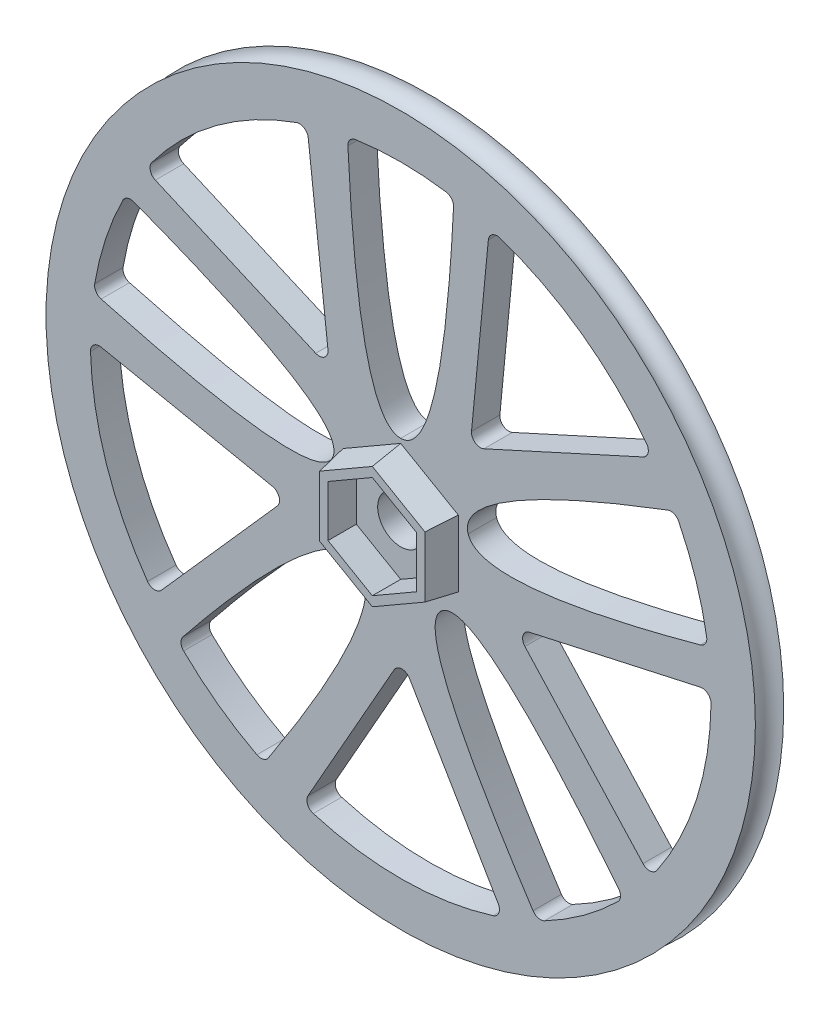
SolidWorks part; units mm, degrees
ref_plane "Front Plane" through (0, 0, 0) normal (0, 0, 1) x (1, 0, 0)
ref_plane "Top Plane" through (0, 0, 0) normal (0, 1, 0) x (1, 0, 0)
ref_plane "Right Plane" through (0, 0, 0) normal (1, 0, 0) x (0, 0, -1)
sketch "Sketch1" plane through (0, 0, 0) normal (0, 0, 1) x (1, 0, 0)
  circle A0 centre (0, 0) radius 50.8
  dimension "D1" = 101.6
extrude "Boss-Extrude1" add sketch "Sketch1" along normal mid plane 4.064
ref_axis "Axis1" through (0, 0, 17.7732) along (0, 0, -1)
sketch "Sketch2" plane through (0, 0, 0) normal (1, 0, 0) x (0, 0, -1)
  line L2 (-2.032, 50.8) -> (-2.032, -50.8) construction
  line L3 (-2.032, 50.8) -> (2.032, 50.8)
  circle A0 centre (0, 50.8) radius 2.032 construction
  arc A1 (-2.032, 50.8) -> (2.032, 50.8) centre (0, 50.8) ccw
revolve "Cut-Revolve1" cut sketch "Sketch2" angle 360 about axis through (0, 0, 17.7732) along (0, 0, -1)
sketch "Sketch3" plane through (0, 0, 0) normal (0, 0, 1) x (1, 0, 0)
  line L0 (0, 0) -> (0, 44.45) construction
  line L1 (0, 0) -> (44.45, 0) construction
  line L2 (-2.8815, 10.16) -> (2.8815, 10.16) construction
  line L3 (2.8814, 10.16) -> (-2.8815, 10.16) construction
  circle A0 centre (0, 0) radius 10.16 construction
  arc A1 (-7.62, 43.792) -> (7.62, 43.792) centre (0, 0) cw
  circle A2 centre (0, 0) radius 44.45 construction
  spline S0 degree 2 poles (0, 10.16) (6.0921, 10.16) (7.62, 43.792) knots 0 0 0 1 1 1
  spline S1 degree 2 poles (0, 10.16) (-6.0921, 10.16) (-7.62, 43.792) knots 0 0 0 1 1 1
  dimension "D1" = 20.32
  dimension "D2" = 88.9
  dimension "D3" = 15.24
extrude "Cut-Extrude1" cut sketch "Sketch3" against normal mid plane 5.08
pattern_circular "CirPattern1" count 5 over 360 about axis through (0, 0, 17.7732) along (0, 0, -1) of "Cut-Extrude1"
sketch "Sketch4" plane through (0, 0, 0) normal (0, 0, 1) x (1, 0, 0)
  line L0 (12.7, 42.5971) -> (9.9317, 13.9168)
  line L1 (9.9317, 13.9168) -> (36.1537, 25.8595)
  circle A0 centre (0, 0) radius 10.16 construction
  circle A1 centre (0, 0) radius 10.16 construction
  circle A2 centre (0, 0) radius 44.45 construction
  circle A3 centre (0, 0) radius 44.45 construction
  arc A4 (12.7, 42.5971) -> (36.1537, 25.8595) centre (0, 0) cw
  dimension "D1" = 5.08
  dimension "D2" = 5.08
  dimension "D3" = 60
extrude "Cut-Extrude2" cut sketch "Sketch4" against normal mid plane 5.08
pattern_circular "CirPattern2" count 5 over 360 about axis through (0, 0, 0) along (0, 0, 1) of "Cut-Extrude2"
fillet "Fillet1" radius 1.27 25 edges at (-16.215, -5.4213, 0) (0.1452, -17.0966, 0) (16.3047, -5.145, 0) (9.9317, 13.9168, 0) (-10.1666, 13.7461, 0) (12.7, 42.5971, 0) (36.1537, 25.8595, 0) (44.0034, 6.2854, 0) (39.2939, 20.7795, 0) (44.4368, 1.0848, 0) (35.766, -26.3932, 0) (31.905, -30.9495, 0) (19.5756, -39.9074, 0) (14.7634, -41.9266, 0) (-14.0491, -42.1714, 0) (-19.5756, -39.9074, 0) (-31.905, -30.9495, 0) (-35.3125, -26.9969, 0) (-44.4488, 0.3298, 0) (-44.0034, 6.2854, 0) (-39.2939, 20.7795, 0) (-36.5877, 25.2416, 0) (-13.4218, 42.3752, 0) (-7.62, 43.792, 0) (7.62, 43.792, 0)
sketch "Sketch5" plane through (0, 0, 2.032) normal (0, 0, 1) x (1, 0, 0)
  line L1 (-8.255, -4.766) -> (0, -9.5321)
  line L2 (0, -9.5321) -> (8.255, -4.766)
  line L3 (8.255, -4.766) -> (8.255, 4.766)
  line L4 (8.255, 4.766) -> (0, 9.5321)
  line L5 (0, 9.5321) -> (-8.255, 4.766)
  line L6 (-8.255, 4.766) -> (-8.255, -4.766)
  line L7 (0, 0) -> (0, 44.45) construction
  circle A0 centre (0, 0) radius 8.255 construction
  dimension "D1" = 16.51
extrude "Boss-Extrude2" add sketch "Sketch5" along normal blind 4.064 draft 10
sketch "Sketch6" plane through (0, 0, 6.096) normal (0, 0, 1) x (1, 0, 0)
  line L0 (0, 0) -> (0, 44.45) construction
  line L1 (0, -7.3323) -> (6.35, -3.6662)
  line L2 (6.35, -3.6662) -> (6.35, 3.6662)
  line L3 (6.35, 3.6662) -> (0, 7.3323)
  line L4 (0, 7.3323) -> (-6.35, 3.6662)
  line L5 (-6.35, 3.6662) -> (-6.35, -3.6662)
  line L6 (-6.35, -3.6662) -> (0, -7.3323)
  circle A0 centre (0, 0) radius 6.35 construction
  dimension "D1" = 12.7
extrude "Cut-Extrude3" cut sketch "Sketch6" against normal up to surface (4.064 mm away) up to face at (32.7566, -10.3365, 2.032)
sketch "Sketch7" plane through (0, 0, 2.032) normal (0, 0, 1) x (1, 0, 0)
  circle A0 centre (0, 0) radius 3.302
  dimension "D1" = 6.604
extrude "Cut-Extrude4" cut sketch "Sketch7" against normal up to next
